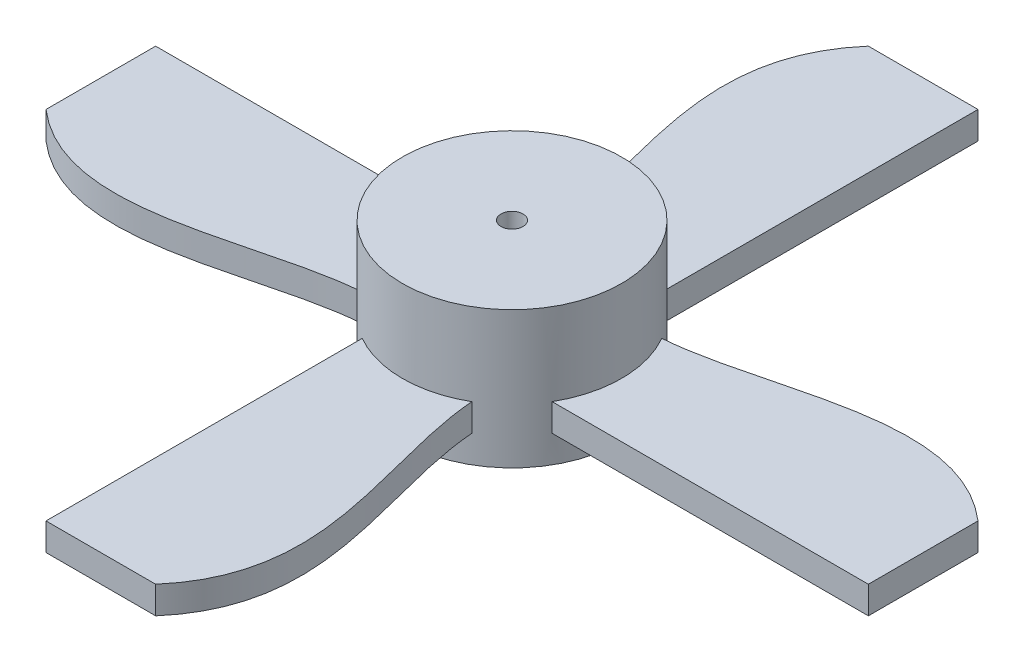
SolidWorks part; units mm, degrees
ref_plane "Front Plane" through (0, 0, 0) normal (0, 0, 1) x (1, 0, 0)
ref_plane "Top Plane" through (0, 0, 0) normal (0, 1, 0) x (1, 0, 0)
ref_plane "Right Plane" through (0, 0, 0) normal (1, 0, 0) x (0, 0, -1)
sketch "Sketch1" plane through (0, 0, 0) normal (0, 1, 0) x (1, 0, 0)
  circle A0 centre (0, 0) radius 4
  dimension "D1" = 8
extrude "Boss-Extrude1" add sketch "Sketch1" along normal blind 5
sketch "Sketch2" plane through (0, 0, 0) normal (0, 1, 0) x (1, 0, 0)
  line L0 (0, 0) -> (15, 0) construction
  line L1 (15, -2) -> (3.4641, -2)
  line L2 (15, 2) -> (3.4641, 2) construction
  line L3 (15, 2) -> (15, 0)
  line L4 (15, 0) -> (15, -2)
  line L5 (2, -15) -> (0, -15)
  line L6 (0, -15) -> (-2, -15)
  line L7 (-2, -15) -> (-2, -3.4641)
  line L8 (-15, -2) -> (-15, 0)
  line L9 (-15, 0) -> (-15, 2)
  line L10 (-15, 2) -> (-3.4641, 2)
  line L11 (-2, 15) -> (0, 15)
  line L12 (0, 15) -> (2, 15)
  line L13 (2, 15) -> (2, 3.4641)
  circle A0 centre (0, 0) radius 4 construction
  arc A1 (3.4641, 2) -> (3.4641, -2) centre (0, 0) ccw construction
  circle A2 centre (0, 0) radius 4
  arc A3 (3.4641, -2) -> (3.4641, 2) centre (0, 0) ccw
  arc A4 (-2, -3.4641) -> (2, -3.4641) centre (0, 0) ccw
  arc A5 (-3.4641, 2) -> (-3.4641, -2) centre (0, 0) ccw
  arc A6 (2, 3.4641) -> (-2, 3.4641) centre (0, 0) ccw
  spline S0 degree 3 poles (3.4641, 2) (7.0599, 2.2619) (11.5494, 4.9954) (15, 2) knots 0 0 0 0 1 1 1 1
  spline S1 degree 3 poles (2, -3.4641) (2.2619, -7.0599) (4.9954, -11.5494) (2, -15) knots 0 0 0 0 1 1 1 1
  spline S2 degree 3 poles (-3.4641, -2) (-7.0599, -2.2619) (-11.5494, -4.9954) (-15, -2) knots 0 0 0 0 1 1 1 1
  spline S3 degree 3 poles (-2, 3.4641) (-2.2619, 7.0599) (-4.9954, 11.5494) (-2, 15) knots 0 0 0 0 1 1 1 1
  point P9 (0, 0)
  point P37 (0, 0)
  dimension "D1" = 15
  dimension "D2" = 2
  dimension "D3" = 2
  dimension "D4" = 0
  dimension "D5" = 4
extrude "Boss-Extrude2" add sketch "Sketch2" along normal blind 1 from offset 1
sketch "Sketch3" plane through (0, 5, 0) normal (0, 1, 0) x (1, 0, 0)
  circle A0 centre (0, 0) radius 0.4
  dimension "D1" = 0.8
extrude "Cut-Extrude1" cut sketch "Sketch3" against normal through all both and the other way through all
